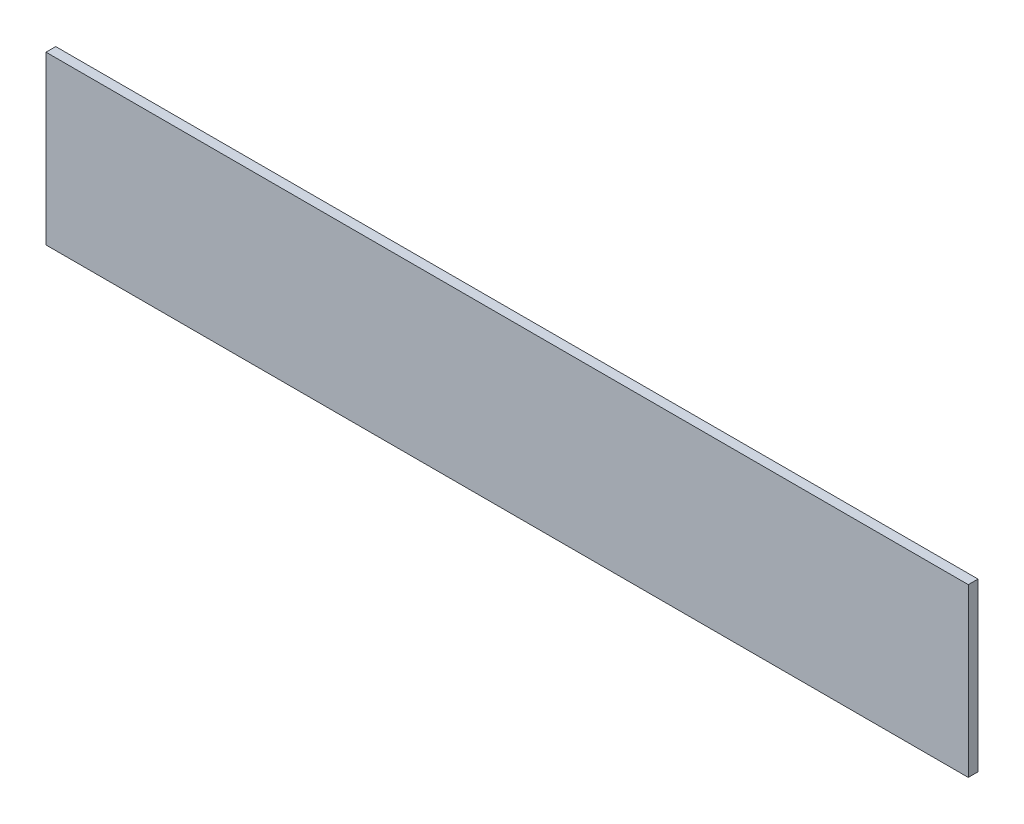
SolidWorks part; units mm, degrees
ref_plane "Front Plane" through (0, 0, 0) normal (0, 0, 1) x (1, 0, 0)
ref_plane "Top Plane" through (0, 0, 0) normal (0, 1, 0) x (1, 0, 0)
ref_plane "Right Plane" through (0, 0, 0) normal (1, 0, 0) x (0, 0, -1)
sketch "Sketch1" plane through (0, 0, 0) normal (0, 0, 1) x (1, 0, 0)
  line L1 (-237.5, -43) -> (237.5, -43)
  line L2 (-237.5, -43) -> (-237.5, 43)
  line L3 (-237.5, 43) -> (237.5, 43)
  line L4 (237.5, -43) -> (237.5, 43)
  line L5 (-237.5, -43) -> (237.5, 43) construction
  line L6 (-237.5, 43) -> (237.5, -43) construction
  point P0 (0, 0)
  dimension "D1" = 475
  dimension "D2" = 86
extrude "Boss-Extrude1" add sketch "Sketch1" along normal blind 5
